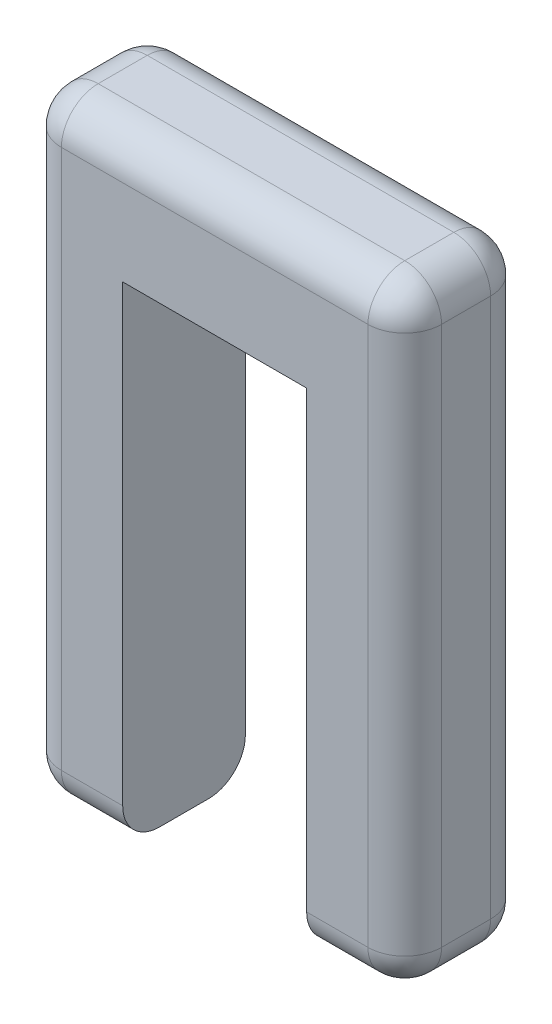
SolidWorks part; units mm, degrees
ref_plane "Front Plane" through (0, 0, 0) normal (0, 0, 1) x (1, 0, 0)
ref_plane "Top Plane" through (0, 0, 0) normal (0, 1, 0) x (1, 0, 0)
ref_plane "Right Plane" through (0, 0, 0) normal (1, 0, 0) x (0, 0, -1)
sketch "Sketch1" plane through (0, 0, 0) normal (0, 0, 1) x (1, 0, 0)
  line L0 (-37.5, -200) -> (-37.5, 0)
  line L1 (-37.5, 0) -> (37.5, 0)
  line L2 (37.5, 0) -> (37.5, -200)
  line L3 (37.5, -200) -> (77.5, -200)
  line L4 (77.5, -200) -> (77.5, 50)
  line L5 (77.5, 50) -> (-77.5, 50)
  line L6 (-77.5, 50) -> (-77.5, -200)
  line L7 (-77.5, -200) -> (-37.5, -200)
  dimension "D1" = 200
  dimension "D2" = 40
  dimension "D3" = 50
  dimension "D4" = 75
extrude "Boss-Extrude1" add sketch "Sketch1" along normal blind 50
fillet "Fillet1" radius 15 14 edges at (-77.5, 50, 25) (0, 50, 0) (77.5, 50, 25) (0, 50, 50) (-77.5, -75, 50) (-77.5, -75, 0) (77.5, -75, 50) (77.5, -75, 0) (-77.5, -200, 25) (-57.5, -200, 50) (-57.5, -200, 0) (57.5, -200, 0) (57.5, -200, 50) (77.5, -200, 25)
